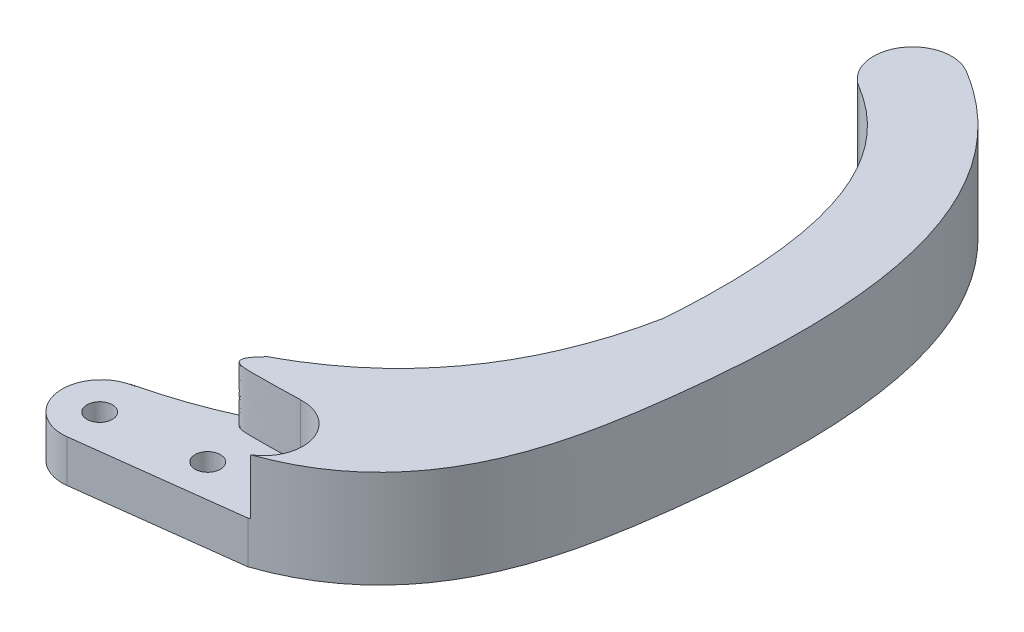
SolidWorks part; units mm, degrees
ref_plane "前视基准面" through (0, 0, 0) normal (0, 0, 1) x (1, 0, 0)
ref_plane "上视基准面" through (0, 0, 0) normal (0, 1, 0) x (1, 0, 0)
ref_plane "右视基准面" through (0, 0, 0) normal (1, 0, 0) x (0, 0, -1)
other "Configuration Table"
sketch "草图1" plane through (0, 0, 0) normal (0, 1, 0) x (1, 0, 0)
  line L0 (-12.0011, -25.7061) -> (-20.0031, -26.7011) construction
  line L5 (-11.5328, -27.6633) -> (-19.7563, -28.6858)
  line L6 (-12.4816, -23.7505) -> (-20.2499, -24.7163)
  arc A4 (-19.7563, -28.6858) -> (-20.2499, -24.7163) centre (-20.0031, -26.7011) cw
  arc A5 (-10.1231, 7.6769) -> (-12.1916, 4.2532) centre (-11.1574, 5.965) ccw
  spline S0 degree 3 poles (-12.0011, -25.7061) (-7.0586, -23.9243) (-5.5073, -17.7477) (-4.037, -1.9563) (-6.9592, 3.4287) (-11.1574, 5.965) knots 0 0 0 0 0.311488 0.411488 1 1 1 1 construction
  spline S1 degree 1 poles (-11.5328, -27.6633) (-10.1231, 7.6769) knots 0 0 1 1 construction
  spline S2 degree 3 poles (-11.5328, -27.6633) (-11.4705, -27.6409) (-11.3551, -27.5995) (-11.0516, -27.4885) (-10.5513, -27.2866) (-9.5849, -26.8294) (-7.8546, -25.7258) (-5.9654, -23.6751) (-4.5564, -20.82) (-3.7319, -17.7967) (-3.2576, -14.743) (-2.9279, -11.6989) (-2.7725, -8.7641) (-2.842, -5.2049) (-3.4251, -1.3182) (-4.9186, 2.5285) (-7.1822, 5.5753) (-9.091, 7.0533) (-10.1231, 7.6769) knots -0.004412 -0.004412 -0.004412 -0.004412 -0.000488 0.003435 0.011282 0.026976 0.058364 0.12114 0.183916 0.246691 0.309467 0.372243 0.435018 0.497794 0.623346 0.748897 0.874449 1 1 1 1
  spline S3 degree 1 poles (-12.4816, -23.7505) (-12.1916, 4.2532) knots 0 0 1 1 construction
  spline S4 degree 3 poles (-12.4816, -23.7505) (-12.2956, -23.678) (-11.9209, -23.5148) (-11.2645, -23.162) (-10.5514, -22.6554) (-9.8376, -21.9461) (-9.0269, -20.8482) (-8.239, -19.1642) (-7.6022, -16.7061) (-7.189, -13.9343) (-6.8936, -11.0878) (-6.773, -8.4706) (-6.8542, -5.3794) (-7.3678, -2.1929) (-8.5146, 0.6565) (-9.829, 2.402) (-11.0949, 3.5319) (-11.8198, 4.0286) (-12.1916, 4.2532) knots 0.005238 0.005238 0.005238 0.005238 0.020781 0.036325 0.067411 0.098497 0.129583 0.191756 0.253929 0.316101 0.378274 0.440447 0.502619 0.626964 0.75131 0.875655 0.937827 1 1 1 1
  dimension "D1" = 2
  dimension "D2" = 2
extrude "凸台-拉伸1" add sketch "草图1" along normal blind 5
ref_plane "基准面1" through (0, 0, 20) normal (0, 0, 1) x (1, 0, 0)
sketch "草图5" plane through (0, 0, 20) normal (0, 0, 1) x (1, 0, 0)
  line L0 (-2.8006, 5) -> (-11.5328, 5) construction
  line L2 (-22.0031, 4.1627) -> (-22.0031, 5)
  line L11 (-22.0031, 5) -> (-10.2768, 5)
  line L13 (-10.2768, 4.1627) -> (-10.2768, 5)
  line L24 (-23.9422, 4.1627) -> (-12.1381, 4.1627) construction
  line L26 (-22.0031, 4.1627) -> (-22.0031, 2.1627)
  line L27 (-22.0031, 2.1627) -> (-10.2768, 2.1627)
  line L29 (-22.0031, 5) -> (-22.0031, 0) construction
  line L31 (-10.2768, 4.1627) -> (-10.2768, 2.1627)
extrude "切除-拉伸3" cut sketch "草图5" along normal through all
sketch "草图6" plane through (0, 5, 0) normal (0, 1, 0) x (1, 0, 0)
  circle A0 centre (-20.0211, -26.7593) radius 0.65
  circle A2 centre (-15.049, -26.2048) radius 0.65
  point P5 (-15.049, -26.2048)
  dimension "D2" = 1.3
  dimension "D4" = 1.3
extrude "切除-拉伸4" cut sketch "草图6" against normal through all
sketch "草图7" plane through (0, 0, 0) normal (0, -1, 0) x (1, 0, 0)
  circle A0 centre (-20.0211, 26.7593) radius 1.25
  circle A2 centre (-15.049, 26.2048) radius 1.25
  dimension "D1" = 2.5
  dimension "D2" = 2.5
extrude "切除-拉伸5" cut sketch "草图7" against normal blind 0.85
sketch "草图8" plane through (0, 2.1627, 0) normal (0, 1, 0) x (1, 0, 0)
  line L0 (-12.4816, -23.7505) -> (-12.5808, -23.9201)
  line L3 (-12.4816, -23.7505) -> (-20.2499, -24.7163)
  line L4 (-19.7563, -28.6858) -> (-11.5328, -27.6633)
  line L5 (-10.2768, -27.1534) -> (-10.2768, -22.3714)
  line L8 (-10.2768, -27.1534) -> (-10.2768, -22.3714)
  arc A1 (-20.2499, -24.7163) -> (-19.7563, -28.6858) centre (-20.0031, -26.7011) ccw
  arc A3 (-12.1381, -27.8895) -> (-12.5808, -23.9201) centre (-12.4679, -25.9169) ccw construction
  arc A4 (-11.4293, -27.626) -> (-12.5808, -23.9201) centre (-12.4679, -25.9169) ccw
  spline S2 degree 3 poles (2615.1457, 1419.2376) (-118.0279, 118.5343) (11.7988, -6.7774) (-11.2645, -23.162) (-21.6691, -28.7529) (-75.5215, -21.7629) (2691.7846, 1274.1909) knots -1.528957 -1.528957 -1.528957 -1.528957 0.937827 0.968914 0.984457 1.923274 1.923274 1.923274 1.923274 only from (-10.2768, -22.3714) to (-12.4816, -23.7505)
  spline S3 degree 3 poles (-2805.4388, -1118.9376) (12.9139, -17.8934) (-15.799, -29.2257) (-11.0516, -27.4885) (16.6925, -16.2901) (-16.4799, 90.017) (-2925.4397, -726.4843) knots -0.234209 -0.234209 -0.234209 -0.234209 -0.000488 0.003435 0.011282 1.522651 1.522651 1.522651 1.522651 only from (-11.5328, -27.6633) to (-10.2768, -27.1534)
  spline S4 degree 3 poles (-10.2768, -22.3714) (-10.3728, -22.4631) (-10.7244, -22.7783) (-11.2645, -23.162) (-11.9209, -23.5148) (-12.2956, -23.678) (-12.4816, -23.7505) knots 0.925594 0.925594 0.925594 0.925594 0.937827 0.968914 0.984457 1 1 1 1
  spline S5 degree 3 poles (-11.4293, -27.626) (-11.4025, -27.6164) (-11.3123, -27.5839) (-11.0516, -27.4885) (-10.6941, -27.3442) (-10.4146, -27.2186) (-10.2768, -27.1534) knots -0.002197 -0.002197 -0.002197 -0.002197 -0.000488 0.003435 0.011282 0.019137 0.019137 0.019137 0.019137
  dimension "D1" = 0
extrude "凸台-拉伸2" add sketch "草图8" along normal up to surface (2.8373 mm away) up to face at (-11.4036, 5, 10.1658)
sketch "草图9" plane through (0, 0, 0) normal (0, -1, 0) x (1, 0, 0)
  line L2 (-11.5328, 27.6633) -> (-19.7563, 28.6858)
  line L3 (-20.2499, 24.7163) -> (-12.4816, 23.7505)
  line L5 (-20.4899, 24.7462) -> (-12.4816, 23.7505)
  arc A2 (-19.7563, 28.6858) -> (-20.2499, 24.7163) centre (-20.0031, 26.7011) ccw
  arc A3 (-12.1916, -4.2532) -> (-10.1231, -7.6769) centre (-11.1574, -5.965) ccw
  spline S0 degree 2 poles (-20.4899, 24.7462) (-9.0856, 22.0034) (-6.9142, 11.0123) knots 0 0 0 1 1 1
  spline S2 degree 3 poles (660.261, -749.6885) (-214.5254, 125.7683) (-34.9416, -42.9385) (-4.9186, -2.5285) (-3.4251, 1.3182) (-2.842, 5.2049) (-2.7725, 8.7641) (-2.9279, 11.6989) (-3.2576, 14.743) (-3.7319, 17.7967) (-4.5564, 20.82) (-5.9654, 23.6751) (-7.8546, 25.7258) (-9.5849, 26.8294) (-10.5513, 27.2866) (-11.0516, 27.4885) (-14.4242, 28.7226) (-1.2843, 23.5089) (-942.7225, 391.2595) knots -4.623335 -4.623335 -4.623335 -4.623335 0.12114 0.246691 0.372243 0.497794 0.56057 0.623346 0.686121 0.748897 0.811673 0.874449 0.937224 0.968612 0.984306 0.992153 0.996077 1.158705 1.158705 1.158705 1.158705 only from (-10.1231, -7.6769) to (-11.5328, 27.6633)
  spline S3 degree 3 poles (2691.8156, -1274.2055) (-75.5219, 21.7628) (-21.6691, 28.7529) (-11.2645, 23.162) (-10.5514, 22.6554) (-9.8376, 21.9461) (-9.0269, 20.8482) (-8.239, 19.1642) (-7.6022, 16.7061) (-7.189, 13.9343) (-6.8936, 11.0878) (-6.773, 8.4706) (-6.8542, 5.3794) (-7.3678, 2.1929) (-8.5146, -0.6565) (-9.829, -2.402) (-29.6078, -20.0562) (-132.8663, 25.2897) (2558.7995, 1539.2725) knots -0.918039 -0.918039 -0.918039 -0.918039 0.020781 0.036325 0.067411 0.098497 0.129583 0.191756 0.253929 0.316101 0.378274 0.440447 0.502619 0.626964 0.75131 0.875655 0.937827 4.636908 4.636908 4.636908 4.636908 only from (-12.4816, 23.7505) to (-12.1916, -4.2532)
  spline S5 degree 3 poles (-12.4816, 23.7505) (-12.2956, 23.678) (-11.9209, 23.5148) (-11.2645, 23.162) (-10.5514, 22.6554) (-9.8376, 21.9461) (-9.0269, 20.8482) (-8.239, 19.1642) (-7.6022, 16.7061) (-7.189, 13.9343) (-6.988, 11.997) (-6.917, 11.0501) (-6.9142, 11.0123) knots 0.005238 0.005238 0.005238 0.005238 0.020781 0.036325 0.067411 0.098497 0.129583 0.191756 0.253929 0.316101 0.378274 0.380868 0.380868 0.380868 0.380868
  dimension "D1" = 0
extrude "凸台-拉伸3" add sketch "草图9" against normal up to surface (2.1627 mm away) up to face at (-20.0211, 2.1627, 27.4093)
sketch "草图10" plane through (0, 2.1627, 0) normal (0, 1, 0) x (1, 0, 0)
  line L0 (-12.4816, -23.7505) -> (-12.5808, -23.9201) construction
  line L1 (-12.4816, -23.7505) -> (-12.5737, -23.908)
  parabola Q2 (-20.4899, -24.7462) -> (-6.9142, -11.0123) focus (-16.4754, -14.3842) apex (-10.874, -19.3882) construction
  parabola Q3 (-15.3526, -22.8528) -> (-6.9142, -11.0123) focus (-16.4754, -14.3842) apex (-10.874, -19.3882)
  spline S0 degree 3 poles (-241.6787, -983.0626) (-53.3616, -2.5778) (-2.8185, 28.1763) (-7.189, -13.9343) (-7.6022, -16.7061) (-8.239, -19.1642) (-9.0269, -20.8482) (-9.8376, -21.9461) (-10.5514, -22.6554) (-11.2645, -23.162) (-18.6903, -27.1523) (-47.5072, -24.8116) (883.3281, 420.4145) knots -2.00803 -2.00803 -2.00803 -2.00803 0.626964 0.689137 0.75131 0.813482 0.875655 0.906741 0.937827 0.968914 0.984457 1.641143 1.641143 1.641143 1.641143 only from (-6.9142, -11.0123) to (-12.4816, -23.7505) construction
  spline S1 degree 3 poles (-6.9142, -11.0123) (-6.917, -11.0501) (-6.988, -11.997) (-7.189, -13.9343) (-7.6022, -16.7061) (-8.239, -19.1642) (-9.0269, -20.8482) (-9.8376, -21.9461) (-10.5514, -22.6554) (-11.2645, -23.162) (-11.9209, -23.5148) (-12.2956, -23.678) (-12.4816, -23.7505) knots 0.624371 0.624371 0.624371 0.624371 0.626964 0.689137 0.75131 0.813482 0.875655 0.906741 0.937827 0.968914 0.984457 1 1 1 1
  spline S2 degree 3 poles (-12.5737, -23.908) (-13.0495, -23.9339) (-14.701, -23.9639) (-16.4269, -23.9491) (-15.3526, -22.8528) knots 0 0 0 0 0.570111 1 1 1 1
extrude "凸台-拉伸4" add sketch "草图10" along normal up to surface (2.8373 mm away) up to face at (-11.9159, 5, 13.1065)
